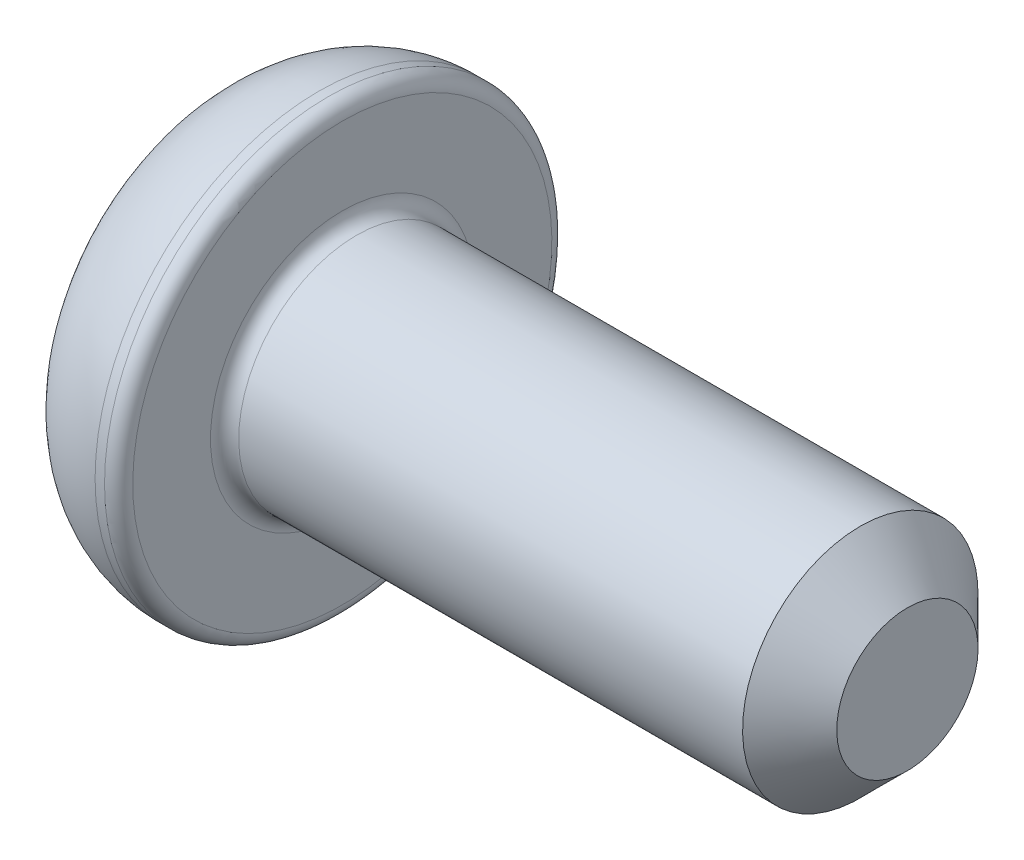
SolidWorks part; units mm, degrees
ref_plane "Спереди" through (0, 0, 0) normal (0, 0, 1) x (1, 0, 0)
ref_plane "Сверху" through (0, 0, 0) normal (0, 1, 0) x (1, 0, 0)
ref_plane "Справа" through (0, 0, 0) normal (1, 0, 0) x (0, 0, -1)
sketch "Эскиз1" plane through (0, 0, 0) normal (0, 0, 1) x (1, 0, 0)
  line L0 (0, 0) -> (0, 3.625)
  line L1 (2.1, 4.75) -> (2.6, 4.75)
  line L2 (2.6, 4.75) -> (2.6, 2.5)
  line L3 (2.6, 2.5) -> (14.6, 2.5)
  line L4 (14.6, 2.5) -> (14.6, 0)
  line L5 (14.6, 0) -> (0, 0) construction
  line L6 (0, 0) -> (14.6, 0)
  arc A0 (0, 3.625) -> (2.1, 4.75) centre (2.1, 2.2275) cw
  point P9 (2.6, 3.625)
  dimension "D1" = 0.5
  dimension "D2" = 5
  dimension "D3" = 9.5
  dimension "D5" = 2.6
  dimension "D6" = 12
revolve "Повернуть1" add sketch "Эскиз1" angle 360 about L5
cosmetic thread "Условное изображение резьбы1" parameters "D2"=4.11
sketch "Эскиз2" plane through (0, 0, 0) normal (-1, 0, 0) x (0, 0, 1)
  line L1 (0.866, 1.5) -> (-0.866, 1.5)
  line L2 (-0.866, 1.5) -> (-1.7321, 0)
  line L3 (-1.7321, 0) -> (-0.866, -1.5)
  line L4 (-0.866, -1.5) -> (0.866, -1.5)
  line L5 (0.866, -1.5) -> (1.7321, 0)
  line L6 (1.7321, 0) -> (0.866, 1.5)
  circle A0 centre (0, 0) radius 1.5 construction
  dimension "D1" = 3
extrude "Вырез-Вытянуть1" cut sketch "Эскиз2" against normal blind 1.5
fillet "Скругление1" radius 0.3 2 edges at (2.6, 2.5, 0) (2.6, 4.75, 0)
chamfer "Фаска1" distance 1 angle 45 1 edges at (14.6, 2.5, 0)
